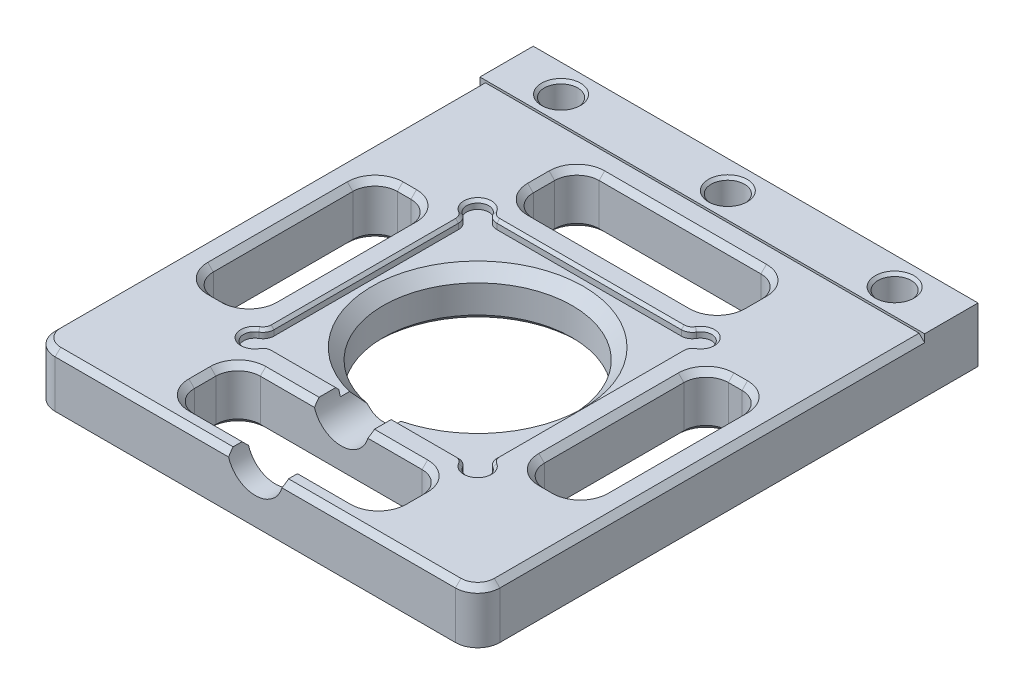
SolidWorks part; units mm, degrees
ref_plane "Front Plane" through (0, 0, 0) normal (0, 0, 1) x (1, 0, 0)
ref_plane "Top Plane" through (0, 0, 0) normal (0, 1, 0) x (1, 0, 0)
ref_plane "Right Plane" through (0, 0, 0) normal (1, 0, 0) x (0, 0, -1)
sketch "Sketch1" plane through (0, 0, 0) normal (0, 1, 0) x (1, 0, 0)
  line L0 (9.025, 10.025) -> (-9.025, 10.025)
  line L1 (10, -10) -> (-10, -10) construction
  line L2 (10, -10) -> (10, 10) construction
  line L3 (10, 10) -> (-10, 10) construction
  line L4 (-10, -10) -> (-10, 10) construction
  line L5 (10, -10) -> (-10, 10) construction
  line L6 (10, 10) -> (-10, -10) construction
  line L7 (-10.025, -9.025) -> (-10.025, 9.025)
  line L8 (9.025, -10.025) -> (-9.025, -10.025)
  line L9 (10.025, -9.025) -> (10.025, 9.025)
  line L10 (10.025, 10.025) -> (-10.025, 10.025) construction
  line L11 (20, -20) -> (-20, -20)
  line L12 (20, -20) -> (20, 20)
  line L13 (20, 20) -> (-20, 20) construction
  line L14 (-20, -20) -> (-20, 20)
  line L15 (20, -20) -> (-20, 20) construction
  line L16 (20, 20) -> (-20, -20) construction
  line L17 (-10.025, -10.025) -> (-10.025, 10.025) construction
  line L18 (10.025, -10.025) -> (10.025, 10.025) construction
  line L19 (10.025, -10.025) -> (-10.025, -10.025) construction
  line L21 (-20, 20) -> (20, 20) construction
  line L22 (-20, 20) -> (-20, 25)
  line L23 (-20, 25) -> (20, 25)
  line L24 (20, 20) -> (20, 25)
  circle A0 centre (0, 0) radius 6
  arc A1 (-9.025, 10.025) -> (-10.025, 9.025) centre (-10.025, 10.025) ccw
  arc A2 (10.025, 9.025) -> (9.025, 10.025) centre (10.025, 10.025) ccw
  arc A3 (9.025, -10.025) -> (10.025, -9.025) centre (10.025, -10.025) ccw
  arc A4 (-10.025, -9.025) -> (-9.025, -10.025) centre (-10.025, -10.025) ccw
  point P0 (0, 0)
  dimension "D4" = 12
  dimension "D6" = 2
  dimension "D1" = 20
  dimension "D2" = 20
  dimension "D5" = 40
  dimension "D7" = 5
  dimension "D3" = 0.025
extrude "Boss-Extrude1" add sketch "Sketch1" along normal blind 0.75 contours L12 L24 L23 L22 L14 L11 A4 L7 A1 L0 A2 L9 A3 L8
sketch "Sketch2" plane through (0, 0, 0) normal (0, -1, 0) x (1, 0, 0)
  line L4 (20, -25) -> (20, 20)
  line L5 (20, 20) -> (-20, 20)
  line L6 (-20, 20) -> (-20, -25)
  line L7 (-20, -25) -> (20, -25)
  line L8 (20, -25) -> (20, 20)
  line L9 (20, 20) -> (-20, 20)
  line L10 (-20, 20) -> (-20, -25)
  line L11 (-20, -25) -> (20, -25)
  circle A0 centre (0, 0) radius 8.5
  dimension "D2" = 17
  dimension "D1" = 0
extrude "Boss-Extrude2" add sketch "Sketch2" along normal blind 4
fillet "Fillet1" radius 1 8 edges at (9.025, 0.375, 10.025) (-9.025, 0.375, 10.025) (-10.025, 0.375, 9.025) (10.025, 0.375, 9.025) (10.025, 0.375, -9.025) (9.025, 0.375, -10.025) (-10.025, 0.375, -9.025) (-9.025, 0.375, -10.025)
sketch "Sketch3" plane through (0, 0.75, 0) normal (0, 1, 0) x (1, 0, 0)
  line L0 (-20, 22.5) -> (20, 22.5) construction
  line L1 (-20, -20) -> (-20, 25) construction
  line L2 (20, -20) -> (20, 25) construction
  line L3 (-20, 25) -> (20, 25) construction
  circle A0 centre (0, 22.5) radius 1.5
  circle A1 centre (-15, 22.5) radius 1.5
  circle A2 centre (15, 22.5) radius 1.5
  dimension "D2" = 3
  dimension "D1" = 2.5
  dimension "D3" = 15
  dimension "D4" = 15
extrude "Cut-Extrude1" cut sketch "Sketch3" against normal blind 7
sketch "Sketch4" plane through (0, 0.75, 0) normal (0, 1, 0) x (1, 0, 0)
  line L0 (20, -20) -> (20, 25) construction
  line L1 (-20, 25) -> (20, 25)
  line L2 (-20, 25) -> (-20, 20.2)
  line L3 (-20, 20.2) -> (20, 20.2)
  line L4 (20, 25) -> (20, 20.2)
  circle A0 centre (15, 22.5) radius 1.5 construction
  circle A1 centre (0, 22.5) radius 1.5 construction
  circle A2 centre (-15, 22.5) radius 1.5 construction
  circle A3 centre (15, 22.5) radius 1.5
  circle A4 centre (0, 22.5) radius 1.5
  circle A5 centre (-15, 22.5) radius 1.5
  dimension "D1" = 4.8
extrude "Boss-Extrude3" add sketch "Sketch4" along normal blind 0.2
chamfer "Chamfer1" distance 0.25 angle 45 3 edges at (15, 0.95, -21) (0, 0.95, -21) (-15, 0.95, -21)
chamfer "Chamfer2" distance 0.25 angle 45 16 edges at (0, 0.75, 10.025) (8.7929, 0.75, 10.159) (-8.7929, 0.75, 10.159) (10.7321, 0.75, 10.7321) (-10.7321, 0.75, 10.7321) (10.159, 0.75, 8.7929) (-10.159, 0.75, 8.7929) (10.025, 0.75, 0) (-10.025, 0.75, 0) (10.159, 0.75, -8.7929) (-10.159, 0.75, -8.7929) (10.7321, 0.75, -10.7321) (-10.7321, 0.75, -10.7321) (8.7929, 0.75, -10.159) (-8.7929, 0.75, -10.159) (0, 0.75, -10.025)
chamfer "Chamfer3" distance 1 angle 45 1 edges at (0, 0, -8.5)
fillet "Fillet2" radius 2 2 edges at (-20, -1.625, 20) (20, -1.625, 20)
ref_plane "Plane1" through (0, -1.625, 0) normal (0, 1, 0) x (1, 0, 0)
chamfer "Chamfer4" distance 0.5 angle 45 5 edges at (20, 0.75, -1.1) (19.4142, 0.75, 19.4142) (0, 0.75, 20) (-19.4142, 0.75, 19.4142) (-20, 0.75, -1.1)
sketch "Sketch5" plane through (0, 0.75, 0) normal (0, 1, 0) x (1, 0, 0)
  line L0 (0, 10.275) -> (0, 20.2) construction
  line L2 (-8.2929, 10.275) -> (8.2929, 10.275) construction
  line L3 (-19.5, 20.2) -> (19.5, 20.2) construction
  line L4 (-10.275, -8.2929) -> (-10.275, 8.2929) construction
  line L5 (9.275, 12.275) -> (-9.275, 12.275)
  line L6 (9.275, 12.275) -> (9.275, 18.2)
  line L7 (9.275, 18.2) -> (-9.275, 18.2)
  line L8 (-9.275, 12.275) -> (-9.275, 18.2)
  line L9 (9.275, 12.275) -> (-9.275, 18.2) construction
  line L10 (9.275, 18.2) -> (-9.275, 12.275) construction
  line L11 (-10.275, 0) -> (-19.5, 0) construction
  line L12 (-19.5, 20.2) -> (-19.5, -18) construction
  line L13 (9.275, -12.275) -> (9.275, -18.2)
  line L14 (-12.275, -8.275) -> (-17.5, -8.275)
  line L15 (-12.275, -8.275) -> (-12.275, 8.275)
  line L16 (-12.275, 8.275) -> (-17.5, 8.275)
  line L17 (-17.5, -8.275) -> (-17.5, 8.275)
  line L18 (-12.275, -8.275) -> (-17.5, 8.275) construction
  line L19 (-12.275, 8.275) -> (-17.5, -8.275) construction
  line L20 (9.275, -12.275) -> (-9.275, -12.275)
  line L21 (-9.275, -12.275) -> (-9.275, -18.2)
  line L22 (9.275, -18.2) -> (-9.275, -18.2)
  line L23 (12.275, -8.275) -> (12.275, 8.275)
  line L24 (12.275, -8.275) -> (17.5, -8.275)
  line L25 (17.5, -8.275) -> (17.5, 8.275)
  line L26 (12.275, 8.275) -> (17.5, 8.275)
  point P7 (0, 15.2375)
  point P19 (-14.8875, 0)
  dimension "D1" = 2
  dimension "D2" = 1
  dimension "D3" = 2
  dimension "D4" = 2
extrude "Cut-Extrude2" cut sketch "Sketch5" against normal blind 11.2
fillet "Fillet3" radius 2 16 edges at (-17.5, -1.625, 8.275) (-17.5, -1.625, -8.275) (-12.275, -1.625, -8.275) (-12.275, -1.625, 8.275) (9.275, -1.625, 12.275) (9.275, -1.625, 18.2) (-9.275, -1.625, 12.275) (-9.275, -1.625, 18.2) (17.5, -1.625, -8.275) (17.5, -1.625, 8.275) (12.275, -1.625, 8.275) (12.275, -1.625, -8.275) (9.275, -1.625, -18.2) (9.275, -1.625, -12.275) (-9.275, -1.625, -12.275) (-9.275, -1.625, -18.2)
chamfer "Chamfer5" distance 0.5 angle 45 68 edges at (15, -4, -24) (0, -4, -24) (-15, -4, -24) (0, -4, -8.5) (-8.6892, -4, 17.6142) (0, -4, 18.2) (-9.275, -4, 15.2375) (8.6892, -4, 17.6142) (-8.6892, -4, 12.8608) (9.275, -4, 15.2375) (0, -4, 12.275) (8.6892, -4, 12.8608) (12.8608, -4, 7.6892) (14.8875, -4, 8.275) (12.275, -4, 0) (16.9142, -4, 7.6892) (12.8608, -4, -7.6892) (17.5, -4, 0) (14.8875, -4, -8.275) (16.9142, -4, -7.6892) (0, -4, -12.275) (-8.6892, -4, -12.8608) (8.6892, -4, -12.8608) (-9.275, -4, -15.2375) (9.275, -4, -15.2375) (-8.6892, -4, -17.6142) (8.6892, -4, -17.6142) (0, -4, -18.2) (-17.5, -4, 0) (-16.9142, -4, -7.6892) (-16.9142, -4, 7.6892) (-14.8875, -4, -8.275) (-14.8875, -4, 8.275) (-12.8608, -4, -7.6892) (-12.8608, -4, 7.6892) (-12.275, -4, 0) (0, 0.75, 18.2) (8.6892, 0.75, 17.6142) (-8.6892, 0.75, 17.6142) (9.275, 0.75, 15.2375) (-9.275, 0.75, 15.2375) (8.6892, 0.75, 12.8608) (-8.6892, 0.75, 12.8608) (0, 0.75, 12.275) (14.8875, 0.75, 8.275) (16.9142, 0.75, 7.6892) (12.8608, 0.75, 7.6892) (17.5, 0.75, 0) (12.275, 0.75, 0) (16.9142, 0.75, -7.6892) (12.8608, 0.75, -7.6892) (14.8875, 0.75, -8.275) (-14.8875, 0.75, 8.275) (-12.8608, 0.75, 7.6892) (-16.9142, 0.75, 7.6892) (-12.275, 0.75, 0) (-17.5, 0.75, 0) (-12.8608, 0.75, -7.6892) (-16.9142, 0.75, -7.6892) (-14.8875, 0.75, -8.275) (0, 0.75, -12.275) (8.6892, 0.75, -12.8608) (-8.6892, 0.75, -12.8608) (9.275, 0.75, -15.2375) (-9.275, 0.75, -15.2375) (8.6892, 0.75, -17.6142) (-8.6892, 0.75, -17.6142) (0, 0.75, -18.2)
sketch "Sketch6" plane through (0, 0, 12.275) normal (0, 0, 1) x (1, 0, 0)
  line L0 (-20, 0.95) -> (20, 0.95) construction
  circle A0 centre (0, 0.95) radius 2.5
  dimension "D1" = 5
extrude "Cut-Extrude3" cut sketch "Sketch6" against normal blind 11.2 and the other way blind 11.2
